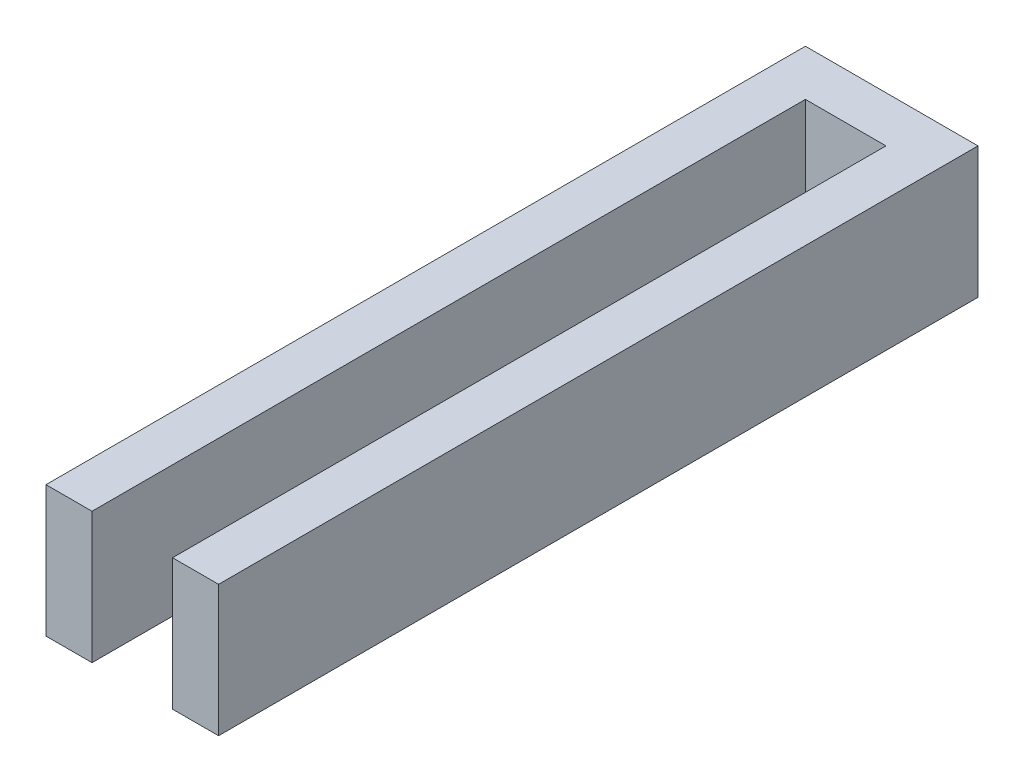
SolidWorks part; units mm, degrees
ref_plane "Alzado" through (0, 0, 0) normal (0, 0, 1) x (1, 0, 0)
ref_plane "Planta" through (0, 0, 0) normal (0, 1, 0) x (1, 0, 0)
ref_plane "Vista lateral" through (0, 0, 0) normal (1, 0, 0) x (0, 0, -1)
sketch "Croquis1" plane through (0, 0, 0) normal (0, 1, 0) x (1, 0, 0)
  line L1 (1.0122, 14.5399) -> (8.5122, 14.5399)
  line L2 (1.0122, 14.5399) -> (1.0122, -18.4601)
  line L3 (1.0122, -18.4601) -> (8.5122, -18.4601)
  line L4 (8.5122, 14.5399) -> (8.5122, -18.4601)
  line L5 (6.5122, -18.4601) -> (3.0122, -18.4601)
  line L6 (6.5122, -18.4601) -> (6.5122, 12.5399)
  line L7 (6.5122, 12.5399) -> (3.0122, 12.5399)
  line L8 (3.0122, -18.4601) -> (3.0122, 12.5399)
  dimension "D1" = 31
  dimension "D2" = 3.5
  dimension "D3" = 2
  dimension "D4" = 2
  dimension "D5" = 2
extrude "Saliente-Extruir1" add sketch "Croquis1" along normal blind 5.7 contours L3 L8 L7 L6 L4 L1 L2
